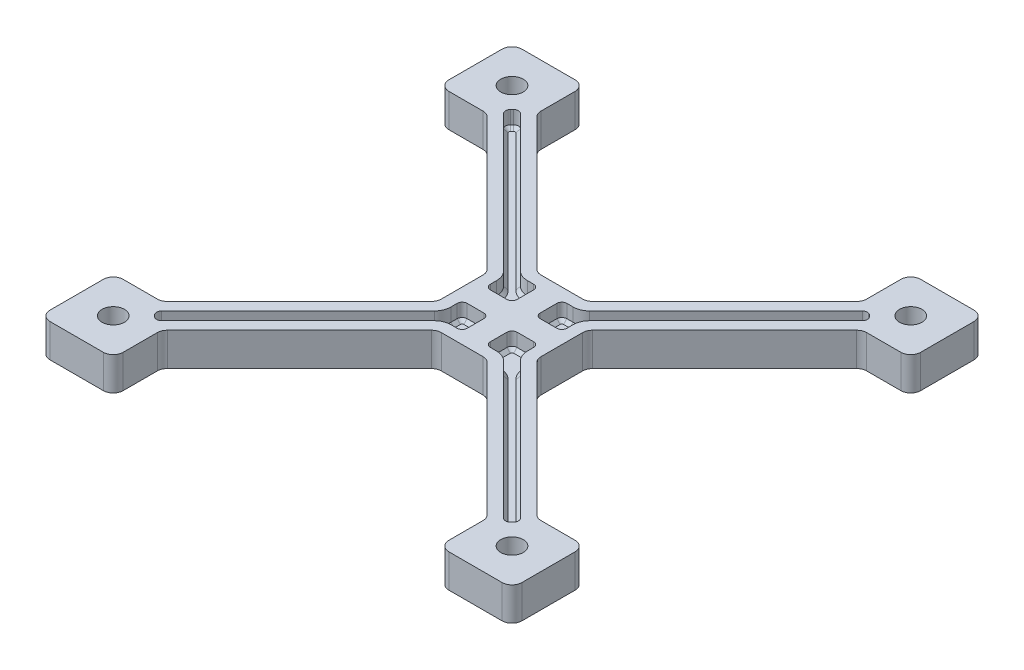
SolidWorks part; units mm, degrees
ref_plane "Front Plane" through (0, 0, 0) normal (0, 0, 1) x (1, 0, 0)
ref_plane "Top Plane" through (0, 0, 0) normal (0, 1, 0) x (1, 0, 0)
ref_plane "Right Plane" through (0, 0, 0) normal (1, 0, 0) x (0, 0, -1)
sketch "Sketch1" plane through (0, 0, 0) normal (0, 1, 0) x (1, 0, 0)
  line L0 (60, 75) -> (60, 60)
  line L1 (0, 0) -> (150, 0) construction
  line L2 (0, 0) -> (0, 150) construction
  line L3 (0, 150) -> (150, 150) construction
  line L4 (150, 0) -> (150, 150) construction
  line L5 (75, 150) -> (75, 0) construction
  line L6 (0, 75) -> (150, 75) construction
  line L7 (60, 60) -> (75, 60)
  line L8 (90, 60) -> (75, 60)
  line L9 (4, 4) -> (26, 4)
  line L10 (18.5, 26) -> (60, 67.5)
  line L11 (26, 18.5) -> (67.5, 60)
  line L12 (4, 4) -> (4, 26)
  line L13 (4, 26) -> (26, 26)
  line L14 (26, 4) -> (26, 26)
  line L15 (15, 26) -> (15, 4) construction
  line L16 (4, 15) -> (26, 15) construction
  line L17 (90, 90) -> (90, 60)
  line L18 (124, 18.5) -> (82.5, 60)
  line L19 (131.5, 26) -> (90, 67.5)
  line L20 (146, 26) -> (124, 26)
  line L21 (124, 4) -> (124, 26)
  line L22 (146, 4) -> (124, 4)
  line L23 (146, 4) -> (146, 26)
  line L24 (4, 135) -> (26, 135) construction
  line L25 (15, 124) -> (15, 146) construction
  line L26 (146, 146) -> (146, 124)
  line L27 (146, 146) -> (124, 146)
  line L28 (124, 146) -> (124, 124)
  line L29 (146, 124) -> (124, 124)
  line L30 (131.5, 124) -> (90, 82.5)
  line L31 (124, 131.5) -> (82.5, 90)
  line L32 (26, 146) -> (26, 124)
  line L33 (4, 124) -> (26, 124)
  line L34 (4, 146) -> (4, 124)
  line L35 (26, 131.5) -> (67.5, 90)
  line L36 (18.5, 124) -> (60, 82.5)
  line L37 (4, 146) -> (26, 146)
  line L38 (90, 90) -> (75, 90)
  line L39 (60, 90) -> (75, 90)
  line L40 (60, 75) -> (60, 90)
  point P4 (15, 15)
  point P5 (135, 15)
  point P6 (135, 135)
  point P7 (15, 135)
  point P12 (15, 15)
  point P20 (60, 67.5)
  point P22 (67.5, 60)
  point P47 (90, 75)
  point P444 (75, 75)
  dimension "D8" = 135
  dimension "D1" = 150
  dimension "D2" = 150
  dimension "D3" = 15
  dimension "D4" = 15
  dimension "D5" = 4
  dimension "D6" = 15
  dimension "D7" = 4
extrude "Boss-Extrude1" add sketch "Sketch1" against normal blind 10 contours L9 L14 L13 L12 | L14 L11 L7 L0 L10 L13 | L40 L0 L7 L8 L17 L38 L39 | L18 L21 L20 L19 L17 L8 | L22 L23 L20 L21 | L29 L26 L27 L28 | L38 L17 L30 L29 L28 L31 | L36 L40 L39 L35 L32 L33 | L37 L34 L33 L32
hole_wizard "1/4 Clearance Hole1" positions "Sketch2" profile "Sketch3" hole size "1/4" standard "ANSI Inch" end condition through all
sketch "Sketch2" plane through (0, 0, 0) normal (0, 1, 0) x (1, 0, 0)
  point P0 (15, 15)
  point P3 (15, 135)
  point P6 (135, 135)
  point P9 (135, 15)
sketch "Sketch3" plane through (15, 0, -15) normal (1, 0, 0) x (0, 0, 1)
  line L0 (0, 0) -> (0, 10)
  line L1 (0, 10) -> (3.3782, 10)
  line L2 (3.3782, 10) -> (3.3782, 0)
  line L5 (3.3782, 0) -> (0, 0)
  line L11 (0, -6.35) -> (0, 107.95) construction
  dimension "Thru Hole Dia." = 6.7564
  dimension "Thru Hole Depth" = 10
sketch "Sketch4" plane through (0, 0, 0) normal (0, 1, 0) x (1, 0, 0)
  line L0 (75, 90) -> (75, 60) construction
  line L1 (82.5, 90) -> (67.5, 90) construction
  line L2 (67.5, 60) -> (82.5, 60) construction
  line L3 (60, 75) -> (90, 75) construction
  line L4 (60, 67.5) -> (60, 82.5) construction
  line L5 (90, 82.5) -> (90, 67.5) construction
  line L27 (86.5, 70) -> (86.5, 68.1213)
  line L28 (85, 71.5) -> (80, 71.5)
  line L29 (78.5, 65) -> (78.5, 70)
  line L30 (81.8787, 63.5) -> (80, 63.5)
  line L31 (126.4393, 21.0104) -> (85.4142, 62.0355)
  line L32 (128.5607, 21.0104) -> (128.9896, 21.4393)
  line L33 (87.9645, 64.5858) -> (128.9896, 23.5607)
  line L34 (62.0355, 64.5858) -> (21.0104, 23.5607)
  line L35 (21.4393, 21.0104) -> (21.0104, 21.4393)
  line L36 (23.5607, 21.0104) -> (64.5858, 62.0355)
  line L37 (68.1213, 63.5) -> (70, 63.5)
  line L38 (71.5, 65) -> (71.5, 70)
  line L39 (65, 71.5) -> (70, 71.5)
  line L40 (63.5, 70) -> (63.5, 68.1213)
  line L41 (63.5, 80) -> (63.5, 81.8787)
  line L42 (65, 78.5) -> (70, 78.5)
  line L43 (71.5, 85) -> (71.5, 80)
  line L44 (68.1213, 86.5) -> (70, 86.5)
  line L45 (23.5607, 128.9896) -> (64.5858, 87.9645)
  line L46 (21.4393, 128.9896) -> (21.0104, 128.5607)
  line L47 (62.0355, 85.4142) -> (21.0104, 126.4393)
  line L59 (128.5607, 128.9896) -> (128.9896, 128.5607)
  line L60 (78.5, 85) -> (78.5, 80)
  line L61 (85, 78.5) -> (80, 78.5)
  line L67 (127.5, 142.5) -> (127.5, 130.0503)
  line L68 (142.5, 142.5) -> (127.5, 142.5)
  line L69 (142.5, 127.5) -> (142.5, 142.5)
  line L70 (130.0503, 127.5) -> (142.5, 127.5)
  line L71 (86.5, 83.9497) -> (130.0503, 127.5)
  line L72 (86.5, 67.5) -> (86.5, 83.9497)
  line L73 (83.9497, 86.5) -> (67.5, 86.5)
  line L74 (127.5, 130.0503) -> (83.9497, 86.5)
  line L79 (87.9645, 85.4142) -> (128.9896, 126.4393)
  line L80 (86.5, 80) -> (86.5, 81.8787)
  line L81 (81.8787, 86.5) -> (80, 86.5)
  line L82 (126.4393, 128.9896) -> (85.4142, 87.9645)
  arc A0 (87.9645, 85.4142) -> (86.5, 81.8787) centre (91.5, 81.8787) ccw
  arc A1 (85.4142, 87.9645) -> (81.8787, 86.5) centre (81.8787, 91.5) cw
  arc A2 (128.9896, 126.4393) -> (128.9896, 128.5607) centre (127.9289, 127.5) ccw
  arc A3 (128.5607, 128.9896) -> (126.4393, 128.9896) centre (127.5, 127.9289) ccw
  arc A4 (86.5, 80) -> (85, 78.5) centre (85, 80) cw
  arc A5 (80, 78.5) -> (78.5, 80) centre (80, 80) cw
  arc A6 (80, 86.5) -> (78.5, 85) centre (80, 85) ccw
  arc A7 (87.9645, 64.5858) -> (86.5, 68.1213) centre (91.5, 68.1213) cw
  arc A8 (86.5, 70) -> (85, 71.5) centre (85, 70) ccw
  arc A9 (80, 71.5) -> (78.5, 70) centre (80, 70) ccw
  arc A10 (80, 63.5) -> (78.5, 65) centre (80, 65) cw
  arc A11 (85.4142, 62.0355) -> (81.8787, 63.5) centre (81.8787, 58.5) ccw
  arc A12 (128.5607, 21.0104) -> (126.4393, 21.0104) centre (127.5, 22.0711) cw
  arc A13 (128.9896, 23.5607) -> (128.9896, 21.4393) centre (127.9289, 22.5) cw
  arc A14 (21.0104, 23.5607) -> (21.0104, 21.4393) centre (22.0711, 22.5) ccw
  arc A15 (21.4393, 21.0104) -> (23.5607, 21.0104) centre (22.5, 22.0711) ccw
  arc A16 (64.5858, 62.0355) -> (68.1213, 63.5) centre (68.1213, 58.5) cw
  arc A17 (70, 63.5) -> (71.5, 65) centre (70, 65) ccw
  arc A18 (70, 71.5) -> (71.5, 70) centre (70, 70) cw
  arc A19 (63.5, 70) -> (65, 71.5) centre (65, 70) cw
  arc A20 (62.0355, 64.5858) -> (63.5, 68.1213) centre (58.5, 68.1213) ccw
  arc A21 (62.0355, 85.4142) -> (63.5, 81.8787) centre (58.5, 81.8787) cw
  arc A22 (63.5, 80) -> (65, 78.5) centre (65, 80) ccw
  arc A23 (70, 78.5) -> (71.5, 80) centre (70, 80) ccw
  arc A24 (70, 86.5) -> (71.5, 85) centre (70, 85) cw
  arc A25 (64.5858, 87.9645) -> (68.1213, 86.5) centre (68.1213, 91.5) ccw
  arc A26 (21.4393, 128.9896) -> (23.5607, 128.9896) centre (22.5, 127.9289) cw
  arc A27 (21.0104, 126.4393) -> (21.0104, 128.5607) centre (22.0711, 127.5) cw
  dimension "D4" = 5
  dimension "D5" = 1.5
  dimension "D2" = 3.5
  dimension "D3" = 3.5
  dimension "D1" = 3.5
extrude "Cut-Extrude1" cut sketch "Sketch4" against normal blind 5
chamfer "Chamfer1" distance 1 angle 45 60 edges at (108.477, -5, -44.0732) (129.4289, -5, -22.5) (128.7751, -5, -21.2249) (127.5, -5, -20.5711) (105.9268, -5, -41.523) (83.7921, -5, -63.1194) (80.9393, -5, -63.5) (78.9393, -5, -63.9393) (78.5, -5, -67.5) (78.9393, -5, -71.0607) (82.5, -5, -71.5) (86.0607, -5, -71.0607) (86.5, -5, -69.0607) (86.8806, -5, -66.2079) (86.5, -5, -80.9393) (86.0607, -5, -78.9393) (82.5, -5, -78.5) (78.9393, -5, -78.9393) (78.5, -5, -82.5) (78.9393, -5, -86.0607) (80.9393, -5, -86.5) (83.7921, -5, -86.8806) (105.9268, -5, -108.477) (127.5, -5, -129.4289) (128.7751, -5, -128.7751) (129.4289, -5, -127.5) (108.477, -5, -105.9268) (86.8806, -5, -83.7921) (41.523, -5, -105.9268) (20.5711, -5, -127.5) (21.2249, -5, -128.7751) (22.5, -5, -129.4289) (44.0732, -5, -108.477) (66.2079, -5, -86.8806) (69.0607, -5, -86.5) (71.0607, -5, -86.0607) (71.5, -5, -82.5) (71.0607, -5, -78.9393) (67.5, -5, -78.5) (63.9393, -5, -78.9393) (63.5, -5, -80.9393) (63.1194, -5, -83.7921) (63.5, -5, -69.0607) (63.9393, -5, -71.0607) (67.5, -5, -71.5) (71.0607, -5, -71.0607) (71.5, -5, -67.5) (71.0607, -5, -63.9393) (69.0607, -5, -63.5) (66.2079, -5, -63.1194) (44.0732, -5, -41.523) (22.5, -5, -20.5711) (21.2249, -5, -21.2249) (20.5711, -5, -22.5) (41.523, -5, -44.0732) (63.1194, -5, -66.2079) (135, -10, -131.6218) (15, -10, -131.6218) (15, -10, -11.6218) (135, -10, -11.6218)
fillet "Fillet1" radius 3 28 edges at (67.5, -5, -90) (82.5, -5, -90) (60, -5, -82.5) (60, -5, -67.5) (67.5, -5, -60) (82.5, -5, -60) (90, -5, -67.5) (90, -5, -82.5) (146, -5, -146) (131.5, -5, -124) (124, -5, -146) (146, -5, -124) (124, -5, -131.5) (18.5, -5, -124) (26, -5, -131.5) (26, -5, -146) (4, -5, -124) (4, -5, -146) (4, -5, -26) (18.5, -5, -26) (4, -5, -4) (26, -5, -18.5) (26, -5, -4) (124, -5, -18.5) (131.5, -5, -26) (146, -5, -26) (124, -5, -4) (146, -5, -4)
